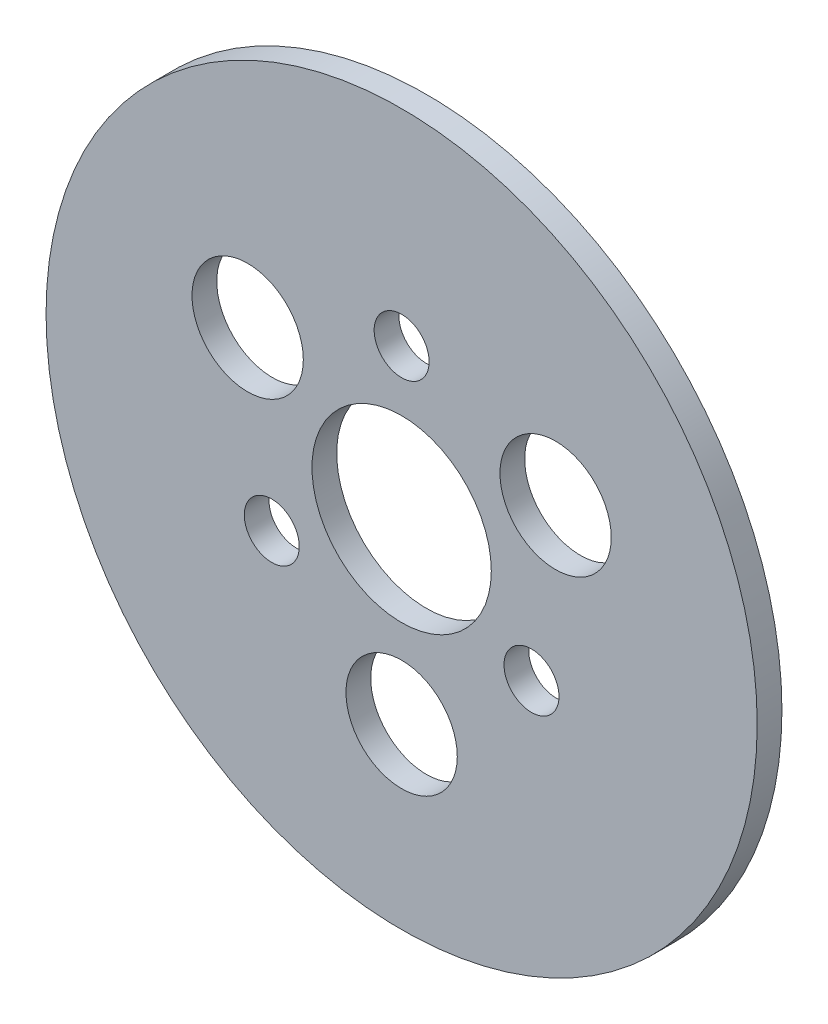
SolidWorks part; units mm, degrees
ref_plane "Front Plane" through (0, 0, 0) normal (0, 0, 1) x (1, 0, 0)
ref_plane "Top Plane" through (0, 0, 0) normal (0, 1, 0) x (1, 0, 0)
ref_plane "Right Plane" through (0, 0, 0) normal (1, 0, 0) x (0, 0, -1)
sketch "Sketch1" plane through (0, 0, 0) normal (0, 0, 1) x (1, 0, 0)
  line L0 (-21, -12.1244) -> (0, 0) construction
  line L1 (0, 0) -> (0, 24.2487) construction
  line L2 (0, 0) -> (21, -12.1244) construction
  line L3 (-21, -12.1244) -> (21, -12.1244) construction
  line L4 (0, 0) -> (0, -28.75) construction
  line L5 (0, 0) -> (-24.8982, 14.375) construction
  line L6 (0, 0) -> (24.8982, 14.375) construction
  line L7 (0, 0) -> (28.75, 0) construction
  line L8 (28.75, 0) -> (57.5, 0) construction
  circle A0 centre (0, 0) radius 57.5
  circle A1 centre (0, 0) radius 14.5
  circle A2 centre (0, 24.2487) radius 4.445
  circle A3 centre (-21, -12.1244) radius 4.445
  circle A4 centre (21, -12.1244) radius 4.445
  circle A5 centre (-24.8982, 14.375) radius 9
  circle A6 centre (24.8982, 14.375) radius 9
  circle A7 centre (0, -28.75) radius 9
  circle A8 centre (0, 0) radius 28.75 construction
  dimension "D1" = 115
  dimension "D2" = 29
  dimension "D6" = 8.89
  dimension "D7" = 18
  dimension "D3" = 120
  dimension "D4" = 120
  dimension "D5" = 42
extrude "Boss-Extrude1" add sketch "Sketch1" along normal mid plane 4
